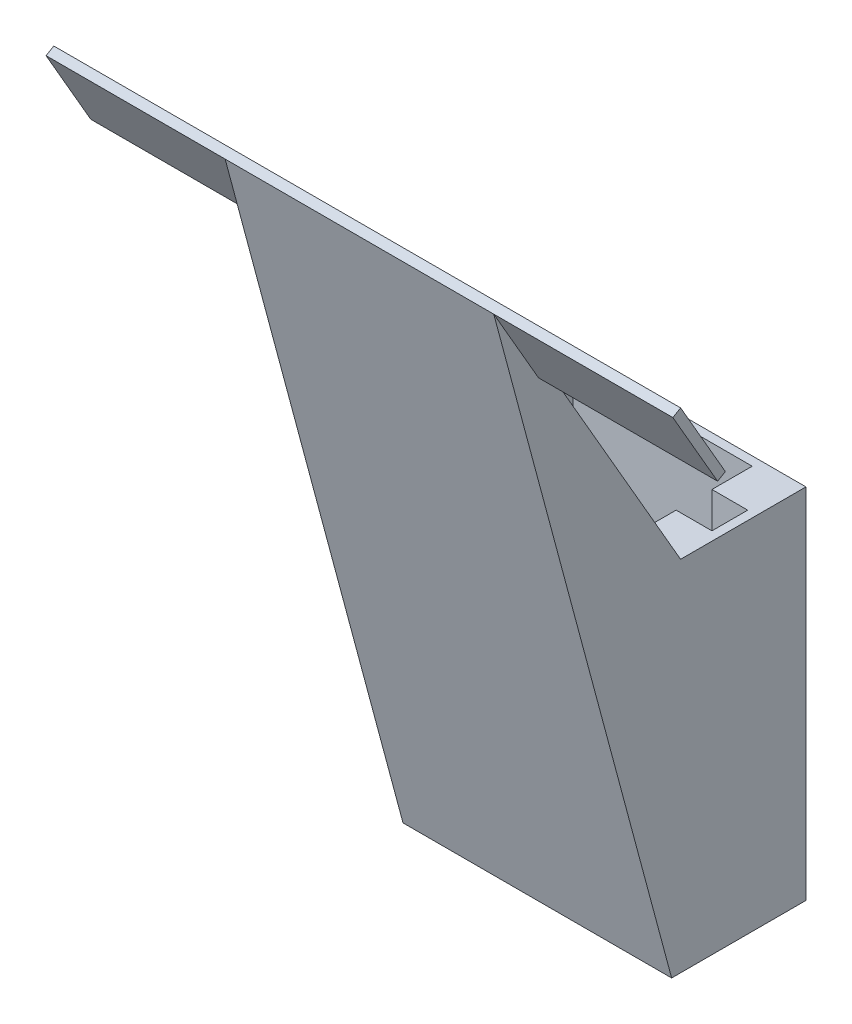
SolidWorks part; units mm, degrees
ref_plane "Ebene vorne" through (0, 0, 0) normal (0, 0, 1) x (1, 0, 0)
ref_plane "Ebene oben" through (0, 0, 0) normal (0, 1, 0) x (1, 0, 0)
ref_plane "Ebene rechts" through (0, 0, 0) normal (1, 0, 0) x (0, 0, -1)
sketch "Skizze1" plane through (0, 0, 0) normal (0, 1, 0) x (1, 0, 0)
  line L0 (-5, 1) -> (-5, 3.25)
  line L1 (5, -3.25) -> (-5, -3.25)
  line L2 (5, -3.25) -> (5, -1)
  line L3 (5, 3.25) -> (-5, 3.25)
  line L4 (-5, -3.25) -> (-5, -1)
  line L5 (5, -3.25) -> (-5, 3.25) construction
  line L6 (5, 3.25) -> (-5, -3.25) construction
  line L7 (7, -1) -> (5, -1)
  line L8 (7, -1) -> (7, 1)
  line L9 (7, 1) -> (5, 1)
  line L10 (-7, -1) -> (-7, 1)
  line L11 (7, -1) -> (-7, 1) construction
  line L12 (7, 1) -> (-7, -1) construction
  line L13 (7.5, -3.75) -> (-7.5, -3.75)
  line L14 (7.5, -3.75) -> (7.5, 3.75)
  line L15 (7.5, 3.75) -> (-7.5, 3.75)
  line L16 (-7.5, -3.75) -> (-7.5, 3.75)
  line L17 (7.5, -3.75) -> (-7.5, 3.75) construction
  line L18 (7.5, 3.75) -> (-7.5, -3.75) construction
  line L19 (-5, 1) -> (-7, 1)
  line L20 (5, 1) -> (5, 3.25)
  line L21 (-5, -1) -> (-7, -1)
  point P0 (0, 0)
  point P5 (0, 0)
  point P11 (0, 0)
  dimension "D1" = 10
  dimension "D2" = 2
  dimension "D3" = 14
  dimension "D4" = 0.5
  dimension "D5" = 0.5
  dimension "D6" = 6.5
extrude "Aufsatz-Linear austragen1" add sketch "Skizze1" along normal blind 20
sketch "Skizze2" plane through (-7.5, 0, 0) normal (-1, 0, 0) x (0, 0, 1)
  line L2 (3.75, 0) -> (3.75, 20)
  line L3 (13.25, 37.3205) -> (13.683, 37.0705)
  line L4 (13.683, 37.0705) -> (3.75, 0)
  line L5 (-3.75, 20) -> (3.75, 20) construction
  line L6 (3.75, 20) -> (3.25, 20)
  line L7 (3.25, 20) -> (13.25, 37.3205)
  point P3 (13.6062, 36.9696)
  dimension "D1" = 0.5
  dimension "D2" = 0.5
  dimension "D3" = 150
  dimension "D4" = 20
extrude "Aufsatz-Linear austragen2" add sketch "Skizze2" against normal up to vertex (15 mm away)
sketch "Skizze4" plane through (-7.5, 0, 0) normal (-1, 0, 0) x (0, 0, 1)
  line L2 (10.75, 32.9904) -> (11.183, 32.7404)
  line L5 (13.25, 37.3205) -> (3.25, 20) construction
  line L6 (10.75, 32.9904) -> (13.25, 37.3205)
  line L7 (13.25, 37.3205) -> (13.683, 37.0705)
  line L8 (13.683, 37.0705) -> (11.183, 32.7404)
  dimension "D1" = 5
extrude "Aufsatz-Linear austragen3" add sketch "Skizze4" along normal blind 10
mirror "Spiegeln3" about plane through (0, 0, 0) normal (1, 0, 0) of "Aufsatz-Linear austragen3"
